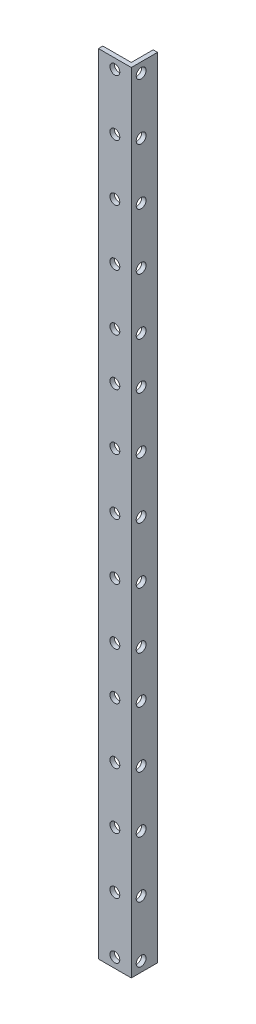
SolidWorks part; units mm, degrees
material "6061-T6 (SS)"
ref_plane "Alzado" through (0, 0, 0) normal (0, 0, 1) x (1, 0, 0)
ref_plane "Planta" through (0, 0, 0) normal (0, 1, 0) x (1, 0, 0)
ref_plane "Vista lateral" through (0, 0, 0) normal (1, 0, 0) x (0, 0, -1)
sketch "Sketch1" plane through (0, 0, 0) normal (0, 1, 0) x (1, 0, 0)
  line L0 (0, 0) -> (15, 0)
  line L1 (15, 0) -> (15, 12)
  line L2 (15, 12) -> (13, 12)
  line L3 (13, 12) -> (13, 2)
  line L4 (13, 2) -> (0, 2)
  line L5 (0, 2) -> (0, 0)
  dimension "D1" = 15
  dimension "D2" = 12
  dimension "D3" = 2
  dimension "D4" = 2
extrude "Boss-Extrude1" add sketch "Sketch1" along normal blind 360
sketch "Sketch2" plane through (13, 0, 0) normal (-1, 0, 0) x (0, 0, 1)
  circle A1 centre (-4.5, 329.8125) radius 2.25
  circle A2 centre (-4.5, 304.125) radius 2.25
  circle A3 centre (-4.5, 278.4375) radius 2.25
  circle A4 centre (-4.5, 252.75) radius 2.25
  circle A5 centre (-4.5, 231.375) radius 2.25
  circle A6 centre (-4.5, 205.6875) radius 2.25
  circle A7 centre (-4.5, 180) radius 2.25
  circle A8 centre (-4.5, 154.3125) radius 2.25
  circle A9 centre (-4.5, 128.625) radius 2.25
  circle A10 centre (-4.5, 107.25) radius 2.25
  circle A11 centre (-4.5, 81.5625) radius 2.25
  circle A12 centre (-4.5, 55.875) radius 2.25
  circle A13 centre (-4.5, 30.1875) radius 2.25
  circle A14 centre (-4.5, 4.5) radius 2.25
  circle A15 centre (-4.5, 355.5) radius 2.25
  dimension "D1" = 4.5
extrude "Cut-Extrude1" cut sketch "Sketch2" against normal up to next
sketch "Sketch3" plane through (0, 0, 0) normal (0, 0, 1) x (1, 0, 0)
  line L0 (-218, 242.75) -> (18, 242.75) construction
  line L2 (18, 363) -> (18, -3) construction
  line L3 (-65, 263) -> (-10, 263) construction
  line L4 (-10, 222.5) -> (-65, 222.5) construction
  line L5 (-218, 117.25) -> (18, 117.25) construction
  line L6 (-218, -3) -> (-218, 363) construction
  line L7 (-65, 137.5) -> (-10, 137.5) construction
  line L8 (-10, 97) -> (-65, 97) construction
  circle A15 centre (7.5, 355.5) radius 2.25
  dimension "D1" = 4.5
extrude "Cut-Extrude2" cut sketch "Sketch3" against normal up to next (2 mm away)
sketch "Sketch4" plane through (0, 0, 0) normal (0, 0, 1) x (1, 0, 0)
  line L0 (18, 242.75) -> (-100, 242.75) construction
  line L1 (-218, 242.75) -> (18, 242.75) construction
  line L2 (18, 117.25) -> (-100, 117.25) construction
  line L3 (-218, 117.25) -> (18, 117.25) construction
pattern_linear "LPattern1" count 5 spacing 25.6562 along (0, -1, 0) of "Cut-Extrude2"
pattern_linear "LPattern2" count 3 spacing 124.1875 along (0, -1, 0) of "LPattern1", "Cut-Extrude2"
